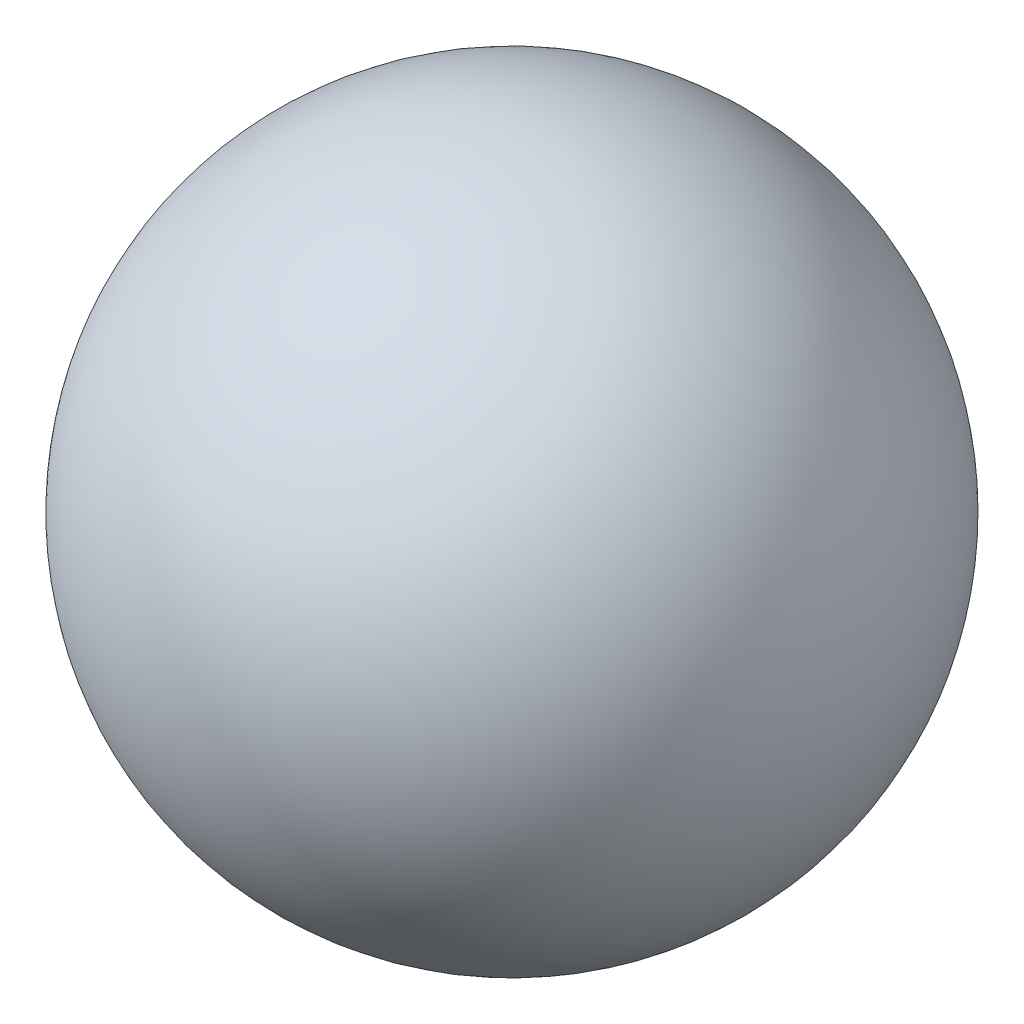
SolidWorks part; units mm, degrees
ref_plane "Front Plane" through (0, 0, 0) normal (0, 0, 1) x (1, 0, 0)
ref_plane "Top Plane" through (0, 0, 0) normal (0, 1, 0) x (1, 0, 0)
ref_plane "Right Plane" through (0, 0, 0) normal (1, 0, 0) x (0, 0, -1)
sketch "Sketch1" plane through (0, 0, 0) normal (1, 0, 0) x (0, 0, -1)
  line L0 (-60.9509, 109.7974) -> (1.3735, 68.0761)
  arc A0 (1.3735, 68.0761) -> (-60.9509, 109.7974) centre (-29.7887, 88.9368) ccw
  dimension "D1" = 75
revolve "Revolve1" add sketch "Sketch1" angle 360 about L0
